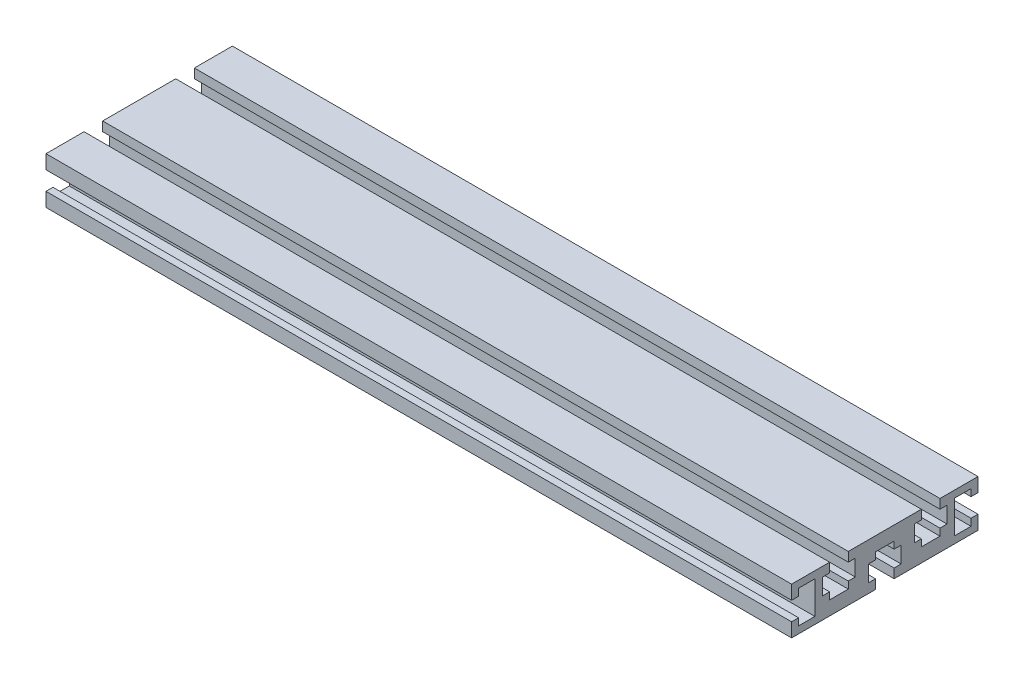
SolidWorks part; units mm, degrees
ref_plane "Front Plane" through (0, 0, 0) normal (0, 0, 1) x (1, 0, 0)
ref_plane "Top Plane" through (0, 0, 0) normal (0, 1, 0) x (1, 0, 0)
ref_plane "Right Plane" through (0, 0, 0) normal (1, 0, 0) x (0, 0, -1)
sketch "Sketch1" plane through (0, 0, 0) normal (1, 0, 0) x (0, 0, -1)
  line L0 (0, 39.6606) -> (0, -35.556) construction
  line L1 (-4, -10.5954) -> (-40, -10.5954)
  line L2 (-40, 3.4046) -> (-37, 3.4046)
  line L3 (15.6832, 9.4046) -> (-15.6832, 9.4046)
  line L4 (-40, -10.5954) -> (-40, -4.5954)
  line L5 (0, 0) -> (-40, 9.4046) construction
  line L6 (0, 0) -> (-40, -10.5954) construction
  line L7 (-37, 3.4046) -> (-37, 6.4046)
  line L8 (-37, 6.4046) -> (-30, 6.4046)
  line L9 (-30, 6.4046) -> (-30, -7.5954)
  line L10 (-30, -7.5954) -> (-37, -7.5954)
  line L11 (-37, -7.5954) -> (-37, -4.5954)
  line L12 (-37, -4.5954) -> (-40, -4.5954)
  line L13 (-15.6832, 9.4046) -> (-15.6832, 5.4046)
  line L14 (-23.6832, 5.4046) -> (-26.6832, 5.4046)
  line L15 (-26.6832, 5.4046) -> (-26.6832, -1.5954)
  line L16 (-26.6832, -1.5954) -> (-23.6832, -1.5954)
  line L17 (-15.6832, -1.5954) -> (-15.6832, -4.5954)
  line L18 (-15.6832, -4.5954) -> (-23.6832, -4.5954)
  line L19 (-23.6832, -4.5954) -> (-23.6832, -1.5954)
  line L20 (-15.6832, -1.5954) -> (-12.6832, -1.5954)
  line L21 (-12.6832, -1.5954) -> (-12.6832, 5.4046)
  line L22 (-12.6832, 5.4046) -> (-15.6832, 5.4046)
  line L23 (-23.6832, 5.4046) -> (-23.6832, 9.4046)
  line L24 (-37, 3.4046) -> (-37, -4.5954) construction
  line L25 (-40, 3.4046) -> (-40, 9.4046)
  line L26 (-23.6832, 9.4046) -> (-40, 9.4046)
  line L27 (-4, 3.4046) -> (4, 3.4046)
  line L28 (-4, -6.5954) -> (-7, -6.5954)
  line L29 (-4, -6.5954) -> (-4, -10.5954)
  line L30 (37, 3.4046) -> (37, -4.5954) construction
  line L31 (0, 0) -> (40, -10.5954) construction
  line L32 (-4, 3.4046) -> (-4, 0.4046)
  line L33 (0, 0) -> (40, 9.4046) construction
  line L34 (7, -6.5954) -> (7, 0.4046)
  line L35 (-7, 0.4046) -> (-4, 0.4046)
  line L36 (-7, -6.5954) -> (-7, 0.4046)
  line L37 (7, 0.4046) -> (4, 0.4046)
  line L38 (4, 3.4046) -> (4, 0.4046)
  line L39 (4, -6.5954) -> (4, -10.5954)
  line L40 (4, -6.5954) -> (7, -6.5954)
  line L41 (23.6832, 9.4046) -> (40, 9.4046)
  line L42 (40, 3.4046) -> (40, 9.4046)
  line L43 (23.6832, 5.4046) -> (23.6832, 9.4046)
  line L44 (12.6832, 5.4046) -> (15.6832, 5.4046)
  line L45 (12.6832, -1.5954) -> (12.6832, 5.4046)
  line L46 (15.6832, -1.5954) -> (12.6832, -1.5954)
  line L47 (23.6832, -4.5954) -> (23.6832, -1.5954)
  line L48 (15.6832, -4.5954) -> (23.6832, -4.5954)
  line L49 (15.6832, -1.5954) -> (15.6832, -4.5954)
  line L50 (26.6832, -1.5954) -> (23.6832, -1.5954)
  line L51 (26.6832, 5.4046) -> (26.6832, -1.5954)
  line L52 (23.6832, 5.4046) -> (26.6832, 5.4046)
  line L53 (15.6832, 9.4046) -> (15.6832, 5.4046)
  line L54 (37, -4.5954) -> (40, -4.5954)
  line L55 (37, -7.5954) -> (37, -4.5954)
  line L56 (30, -7.5954) -> (37, -7.5954)
  line L57 (30, 6.4046) -> (30, -7.5954)
  line L58 (37, 6.4046) -> (30, 6.4046)
  line L59 (37, 3.4046) -> (37, 6.4046)
  line L60 (40, -10.5954) -> (40, -4.5954)
  line L61 (40, 3.4046) -> (37, 3.4046)
  line L62 (4, -10.5954) -> (40, -10.5954)
  point P0 (0, 0)
  point P8 (37, -0.5954)
  point P19 (-37, -0.5954)
  point P34 (0, 3.4046)
  point P42 (0, 3.4046)
  point P48 (0, 3.4046)
  point P66 (0, 9.4046)
  dimension "D2" = 20
  dimension "D3" = 8
  dimension "D4" = 14
  dimension "D5" = 4
  dimension "D6" = 7
  dimension "D7" = 3
  dimension "D8" = 3
  dimension "D9" = 7
  dimension "D10" = 14
  dimension "D11" = 8
  dimension "D12" = 10
extrude "Boss-Extrude1" add sketch "Sketch1" along normal blind 320
